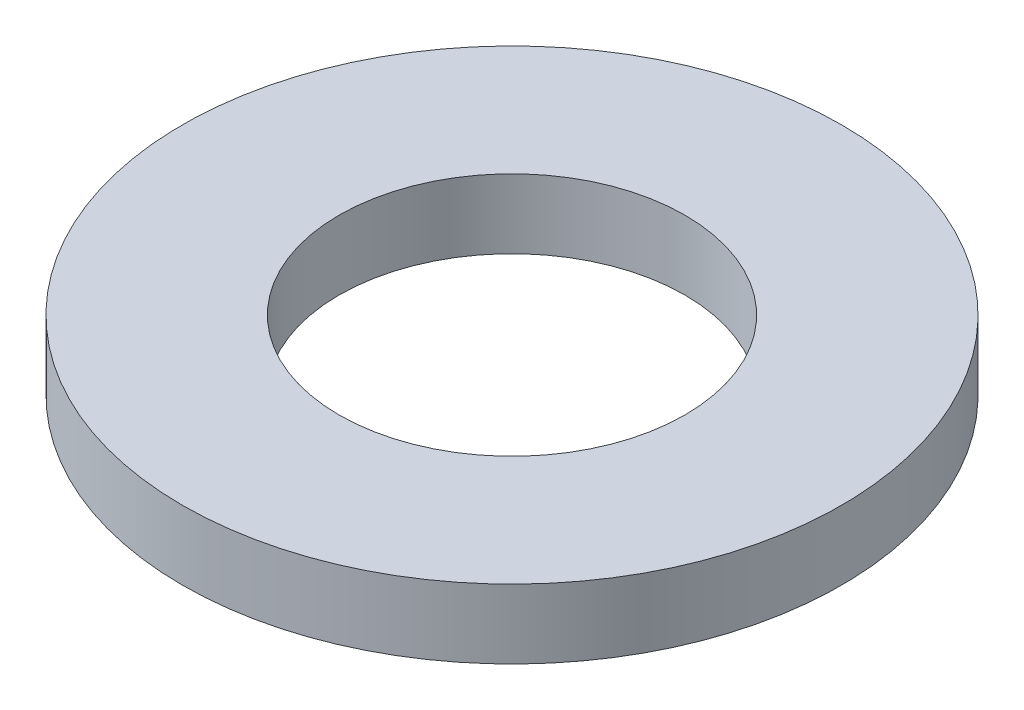
SolidWorks part; units mm, degrees
ref_plane "Front Plane" through (0, 0, 0) normal (0, 0, 1) x (1, 0, 0)
ref_plane "Top Plane" through (0, 0, 0) normal (0, 1, 0) x (1, 0, 0)
ref_plane "Right Plane" through (0, 0, 0) normal (1, 0, 0) x (0, 0, -1)
sketch "Sketch1" plane through (0, 0, 0) normal (0, 1, 0) x (1, 0, 0)
  circle A0 centre (0, 0) radius 2.5
  circle A1 centre (0, 0) radius 4.7625
  dimension "D1" = 5
  dimension "D2" = 9.525
extrude "Boss-Extrude1" add sketch "Sketch1" along normal blind 1
